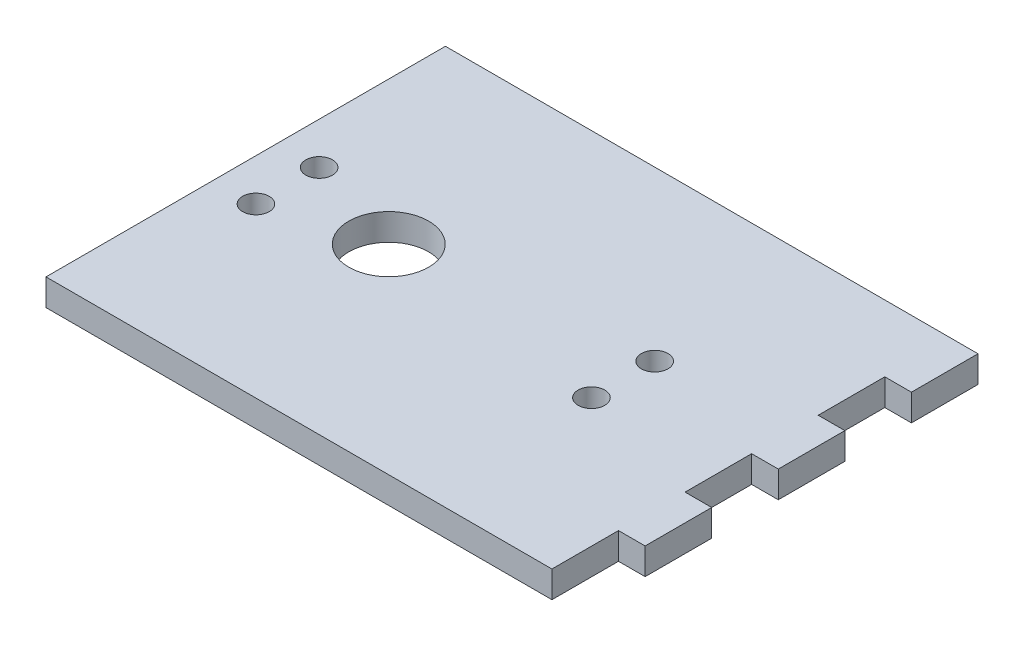
SolidWorks part; units mm, degrees
material "1060 Alloy"
ref_plane "Front Plane" through (0, 0, 0) normal (0, 0, 1) x (1, 0, 0)
ref_plane "Top Plane" through (0, 0, 0) normal (0, 1, 0) x (1, 0, 0)
ref_plane "Right Plane" through (0, 0, 0) normal (1, 0, 0) x (0, 0, -1)
sketch "Sketch1" plane through (0, 0, 0) normal (0, 1, 0) x (1, 0, 0)
  line L2 (-9707.9187, 15348.5094) -> (-9631.9187, 15348.5094)
  line L3 (-9707.9187, 15348.5094) -> (-9707.9187, 15408.5094)
  line L4 (-9707.9187, 15408.5094) -> (-9627.9187, 15408.5094)
  line L5 (-9627.9187, 15358.5054) -> (-9627.9187, 15368.5094)
  line L6 (-9707.9187, 15348.5094) -> (-9627.9187, 15408.5094) construction
  line L7 (-9707.9187, 15408.5094) -> (-9627.9187, 15348.5094) construction
  line L12 (-9627.9187, 15398.5094) -> (-9631.9187, 15398.5094)
  line L13 (-9631.9187, 15398.5094) -> (-9631.9187, 15388.5094)
  line L14 (-9631.9187, 15388.5094) -> (-9627.9187, 15388.5094)
  line L15 (-9627.9187, 15378.5094) -> (-9631.9187, 15378.5094)
  line L16 (-9631.9187, 15378.5094) -> (-9631.9187, 15368.5094)
  line L17 (-9631.9187, 15368.5094) -> (-9627.9187, 15368.5094)
  line L18 (-9627.9187, 15358.5054) -> (-9631.9187, 15358.5054)
  line L19 (-9631.9187, 15358.5054) -> (-9631.9187, 15348.5094)
  line L20 (-9627.9187, 15398.5094) -> (-9627.9187, 15408.5094)
  line L21 (-9627.9187, 15378.5094) -> (-9627.9187, 15388.5094)
  circle A0 centre (-9686.4343, 15378.5094) radius 6
  circle A7 centre (-9651.2343, 15383.2594) radius 2
  circle A8 centre (-9651.2343, 15373.7594) radius 2
  circle A9 centre (-9701.6343, 15373.7594) radius 2
  circle A10 centre (-9701.6343, 15383.2594) radius 2
  point P1 (-9667.9187, 15378.5094)
  dimension "D3" = 12
  dimension "D5" = 10
  dimension "D1" = 60
  dimension "D2" = 80
  dimension "D16" = 10
  dimension "D17" = 10
  dimension "D18" = 10.004
  dimension "D19" = 4
extrude "Boss-Extrude1" add sketch "Sketch1" along normal blind 4
